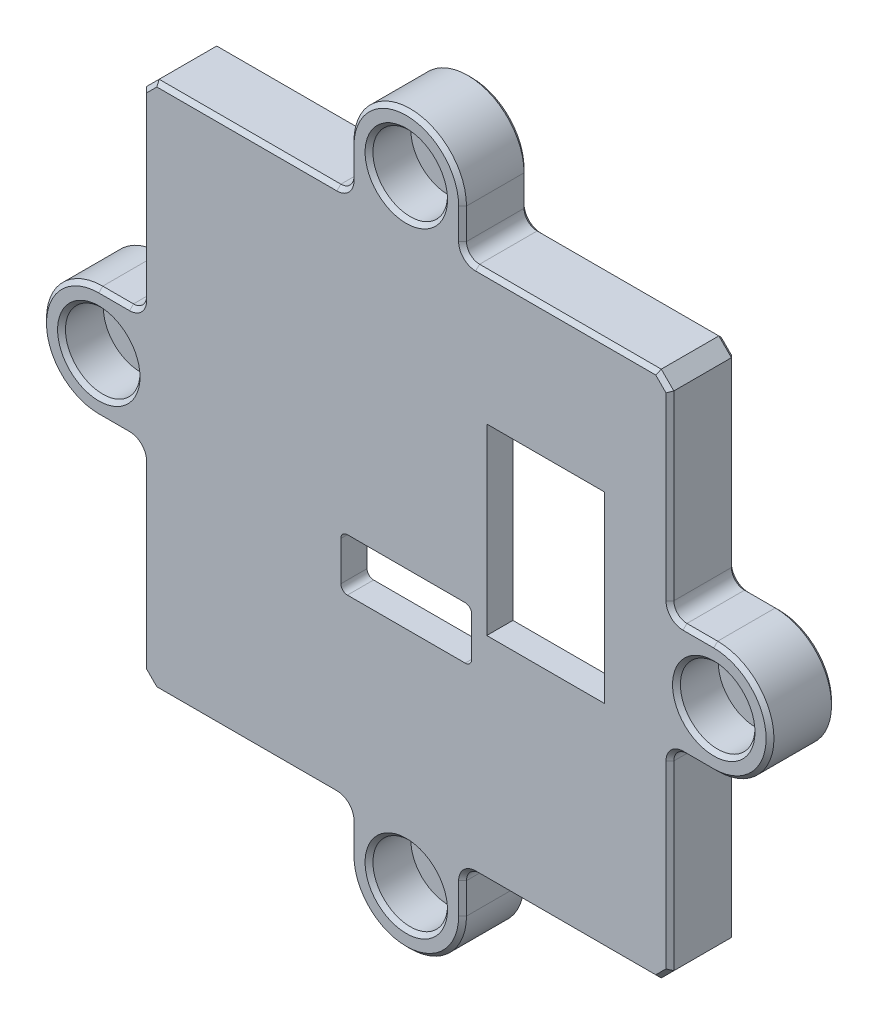
SolidWorks part; units mm, degrees
ref_plane "Front Plane" through (0, 0, 0) normal (0, 0, 1) x (1, 0, 0)
ref_plane "Top Plane" through (0, 0, 0) normal (0, 1, 0) x (1, 0, 0)
ref_plane "Right Plane" through (0, 0, 0) normal (1, 0, 0) x (0, 0, -1)
sketch "Sketch1" plane through (0, 0, 0) normal (0, 0, 1) x (1, 0, 0)
  line L0 (19.1883, 20.15) -> (20.15, 19.1883)
  line L1 (-19.1883, -20.15) -> (-4.3, -20.15)
  line L2 (-20.15, -19.1883) -> (-20.15, -4.3)
  line L3 (-19.1883, 20.15) -> (-4.3, 20.15)
  line L4 (20.15, -19.1883) -> (20.15, -4.3)
  line L5 (-19.6692, -19.6692) -> (19.6692, 19.6692) construction
  line L6 (-19.6692, 19.6692) -> (19.6692, -19.6692) construction
  line L7 (0, 0) -> (0, 8.4657) construction
  line L8 (0, 0) -> (17.8235, 0) construction
  line L9 (-19.1883, 20.15) -> (-20.15, 19.1883)
  line L10 (19.1883, -20.15) -> (20.15, -19.1883)
  line L11 (-19.1883, -20.15) -> (-20.15, -19.1883)
  line L12 (-20.15, 19.1883) -> (-20.15, 20.15) construction
  line L13 (-20.15, 20.15) -> (-19.6692, 19.6692) construction
  line L14 (-20.15, 20.15) -> (-19.1883, 20.15) construction
  line L15 (19.1883, 20.15) -> (20.15, 20.15) construction
  line L16 (19.6692, 19.6692) -> (20.15, 20.15) construction
  line L17 (20.15, 19.1883) -> (20.15, 20.15) construction
  line L18 (20.15, -20.15) -> (20.15, -19.1883) construction
  line L19 (19.6692, -19.6692) -> (20.15, -20.15) construction
  line L20 (19.1883, -20.15) -> (20.15, -20.15) construction
  line L21 (-20.15, -20.15) -> (-20.15, -19.1883) construction
  line L22 (-20.15, -20.15) -> (-19.6692, -19.6692) construction
  line L23 (-20.15, -20.15) -> (-19.1883, -20.15) construction
  line L24 (4.3, 23.5) -> (4.3, 20.15)
  line L25 (-4.3, 23.5) -> (-4.3, 20.15)
  line L26 (23.5, -4.3) -> (20.15, -4.3)
  line L27 (23.5, 4.3) -> (20.15, 4.3)
  line L28 (-4.3, -23.5) -> (-4.3, -20.15)
  line L29 (4.3, -23.5) -> (4.3, -20.15)
  line L30 (-23.5, 4.3) -> (-20.15, 4.3)
  line L31 (-23.5, -4.3) -> (-20.15, -4.3)
  line L32 (-4.3, 20.15) -> (4.3, 20.15) construction
  line L33 (4.3, 20.15) -> (19.1883, 20.15)
  line L34 (20.15, -4.3) -> (20.15, 4.3) construction
  line L35 (20.15, 4.3) -> (20.15, 19.1883)
  line L36 (-20.15, -4.3) -> (-20.15, 4.3) construction
  line L37 (-20.15, 4.3) -> (-20.15, 19.1883)
  line L38 (-4.3, -20.15) -> (4.3, -20.15) construction
  line L39 (4.3, -20.15) -> (19.1883, -20.15)
  line L40 (0, 0) -> (0, -2.5) construction
  line L41 (6.15, -3.85) -> (15.15, -3.85)
  line L42 (6.15, -3.85) -> (6.15, 10.15)
  line L43 (6.15, 10.15) -> (15.15, 10.15)
  line L44 (15.15, -3.85) -> (15.15, 10.15)
  line L46 (-5, -2.5) -> (5, -2.5)
  line L47 (-5, -2.5) -> (-5, -6.5)
  line L48 (-5, -6.5) -> (5, -6.5)
  line L49 (5, -2.5) -> (5, -6.5)
  arc A0 (-4.3, 23.5) -> (4.3, 23.5) centre (0, 23.5) cw
  arc A1 (23.5, -4.3) -> (23.5, 4.3) centre (23.5, 0) ccw
  arc A2 (4.3, -23.5) -> (-4.3, -23.5) centre (0, -23.5) cw
  arc A3 (-23.5, 4.3) -> (-23.5, -4.3) centre (-23.5, 0) ccw
  circle A4 centre (0, 23.5) radius 1.75
  circle A6 centre (23.5, 0) radius 1.75
  circle A7 centre (0, -23.5) radius 1.75
  circle A8 centre (-23.5, 0) radius 1.75
  point P0 (0, 0)
  dimension "D3" = 4.3
  dimension "D4" = 3.5
  dimension "D1" = 40.3
  dimension "D2" = 0.68
  dimension "D5" = 14
  dimension "D6" = 9
  dimension "D7" = 4
  dimension "D8" = 10
  dimension "D9" = 2.5
  dimension "D10" = 10
  dimension "D11" = 5
extrude "Boss-Extrude1" add sketch "Sketch1" along normal blind 5
fillet "Fillet3" radius 0.5 4 edges at (5, -6.5, 2.5) (-5, -6.5, 2.5) (-5, -2.5, 2.5) (5, -2.5, 2.5)
sketch "Sketch2" plane through (0, 0, 5) normal (0, 0, 1) x (1, 0, 0)
  line L0 (0, 0) -> (17.5453, 17.5453) construction
  line L1 (0, 0) -> (12.7197, -12.7197) construction
  circle A0 centre (0, 23.5) radius 2.85
  circle A1 centre (23.5, 0) radius 2.85
  circle A2 centre (-23.5, 0) radius 2.85
  circle A3 centre (0, -23.5) radius 2.85
  dimension "D1" = 5.7
extrude "Cut-Extrude1" cut sketch "Sketch2" against normal blind 3.2
sketch "Sketch3" plane through (0, 0, 1.8) normal (0, 0, 1) x (1, 0, 0)
  circle A0 centre (0, 23.5) radius 2.4072
  circle A1 centre (23.5, 0) radius 2.3403
  circle A2 centre (0, -23.5) radius 2.4119
  circle A3 centre (-23.5, 0) radius 2.4132
extrude "Boss-Extrude2" add sketch "Sketch3" against normal blind 0.2
sketch "Sketch4" plane through (0, 0, 0) normal (0, 0, -1) x (-1, 0, 0)
  line L1 (-17.5, -17.5) -> (17.5, -17.5)
  line L2 (-17.5, -17.5) -> (-17.5, 17.5)
  line L3 (-17.5, 17.5) -> (17.5, 17.5)
  line L4 (17.5, -17.5) -> (17.5, 17.5)
  line L5 (-17.5, -17.5) -> (17.5, 17.5) construction
  line L6 (-17.5, 17.5) -> (17.5, -17.5) construction
  point P0 (0, 0)
  dimension "D1" = 35
extrude "Cut-Extrude2" cut sketch "Sketch4" against normal blind 4
sketch "Sketch5" plane through (0, 0, 4) normal (0, 0, -1) x (-1, 0, 0)
  line L1 (-15.15, 10.15) -> (-6.15, 10.15)
  line L2 (-15.15, 10.15) -> (-15.15, -3.85)
  line L3 (-15.15, -3.85) -> (-6.15, -3.85)
  line L4 (-6.15, 10.15) -> (-6.15, -3.85)
  line L5 (-16.15, 11.15) -> (-5.15, 11.15)
  line L6 (-16.15, 11.15) -> (-16.15, -4.85)
  line L7 (-16.15, -4.85) -> (-6, -4.85)
  line L8 (-5.15, 11.15) -> (-5.15, -1.5)
  line L9 (5, -3) -> (5, -6) construction
  line L11 (-6.15, 10.15) -> (-6.15, -3.85) construction
  line L12 (4.5, -6.5) -> (-4.5, -6.5) construction
  line L13 (-5, -6) -> (-5, -3) construction
  line L14 (-4.5, -2.5) -> (4.5, -2.5) construction
  line L15 (5, -3) -> (5, -6)
  line L16 (4.5, -6.5) -> (-4.5, -6.5)
  line L17 (-5, -6) -> (-5, -3)
  line L18 (-4.5, -2.5) -> (4.5, -2.5)
  line L19 (-5.15, -1.5) -> (6, -1.5)
  line L20 (6, -1.5) -> (6, -7.5)
  line L21 (6, -7.5) -> (-6, -7.5)
  line L22 (-6, -7.5) -> (-6, -4.85)
  arc A0 (5, -3) -> (4.5, -2.5) centre (4.5, -3) ccw construction
  arc A1 (4.5, -6.5) -> (5, -6) centre (4.5, -6) ccw construction
  arc A2 (-5, -6) -> (-4.5, -6.5) centre (-4.5, -6) ccw construction
  arc A3 (-4.5, -2.5) -> (-5, -3) centre (-4.5, -3) ccw construction
  arc A4 (5, -3) -> (4.5, -2.5) centre (4.5, -3) ccw
  arc A5 (4.5, -6.5) -> (5, -6) centre (4.5, -6) ccw
  arc A6 (-5, -6) -> (-4.5, -6.5) centre (-4.5, -6) ccw
  arc A7 (-4.5, -2.5) -> (-5, -3) centre (-4.5, -3) ccw
  dimension "D1" = 1
  dimension "D2" = 1
  dimension "D3" = 1
  dimension "D4" = 1
  dimension "D5" = 1
  dimension "D6" = 1
  dimension "D7" = 1
  dimension "D8" = 1
extrude "Boss-Extrude3" add sketch "Sketch5" along normal blind 1
fillet "Fillet2" radius 1 8 edges at (-20.15, -4.3, 2.5) (-20.15, 4.3, 2.5) (-4.3, 20.15, 2.5) (4.3, 20.15, 2.5) (20.15, 4.3, 2.5) (20.15, -4.3, 2.5) (4.3, -20.15, 2.5) (-4.3, -20.15, 2.5)
fillet "Fillet1" radius 2 4 edges at (-17.5, -17.5, 2) (17.5, -17.5, 2) (17.5, 17.5, 2) (-17.5, 17.5, 2)
chamfer "Chamfer1" distance 0.3 angle 45 80 edges at (-26.35, 0, 5) (2.85, 23.5, 5) (20.65, 0, 5) (2.85, -23.5, 5) (19.6692, 19.6692, 5) (20.15, 12.2442, 5) (22.325, 4.3, 5) (27.8, 0, 5) (22.325, -4.3, 5) (20.15, -12.2442, 5) (19.6692, -19.6692, 5) (12.2442, -20.15, 5) (4.3, -22.325, 5) (0, -27.8, 5) (-4.3, -22.325, 5) (-12.2442, -20.15, 5) (-19.6692, -19.6692, 5) (-20.15, -12.2442, 5) (-22.325, -4.3, 5) (-27.8, 0, 5) (-22.325, 4.3, 5) (-20.15, 12.2442, 5) (-19.6692, 19.6692, 5) (-12.2442, 20.15, 5) (-4.3, 22.325, 5) (0, 27.8, 5) (4.3, 22.325, 5) (12.2442, 20.15, 5) (-25.25, 0, 0) (1.75, -23.5, 0) (21.75, 0, 0) (1.75, 23.5, 0) (4.3, 22.325, 0) (0, 27.8, 0) (-4.3, 22.325, 0) (-12.2442, 20.15, 0) (-19.6692, 19.6692, 0) (-20.15, 12.2442, 0) (-22.325, 4.3, 0) (-27.8, 0, 0) (-22.325, -4.3, 0) (-20.15, -12.2442, 0) (-19.6692, -19.6692, 0) (-12.2442, -20.15, 0) (-4.3, -22.325, 0) (0, -27.8, 0) (4.3, -22.325, 0) (12.2442, -20.15, 0) (19.6692, -19.6692, 0) (20.15, -12.2442, 0) (22.325, -4.3, 0) (27.8, 0, 0) (22.325, 4.3, 0) (20.15, 12.2442, 0) (19.6692, 19.6692, 0) (12.2442, 20.15, 0) (16.9142, 16.9142, 0) (17.5, 0, 0) (16.9142, -16.9142, 0) (0, -17.5, 0) (-16.9142, -16.9142, 0) (-17.5, 0, 0) (-16.9142, 16.9142, 0) (0, 17.5, 0) (20.4429, 4.5929, 5) (20.4429, -4.5929, 5) (4.5929, -20.4429, 5) (-4.5929, -20.4429, 5) (-20.4429, -4.5929, 5) (-20.4429, 4.5929, 5) (-4.5929, 20.4429, 5) (4.5929, 20.4429, 5) (4.5929, 20.4429, 0) (-4.5929, 20.4429, 0) (-20.4429, 4.5929, 0) (-20.4429, -4.5929, 0) (-4.5929, -20.4429, 0) (4.5929, -20.4429, 0) (20.4429, -4.5929, 0) (20.4429, 4.5929, 0)
